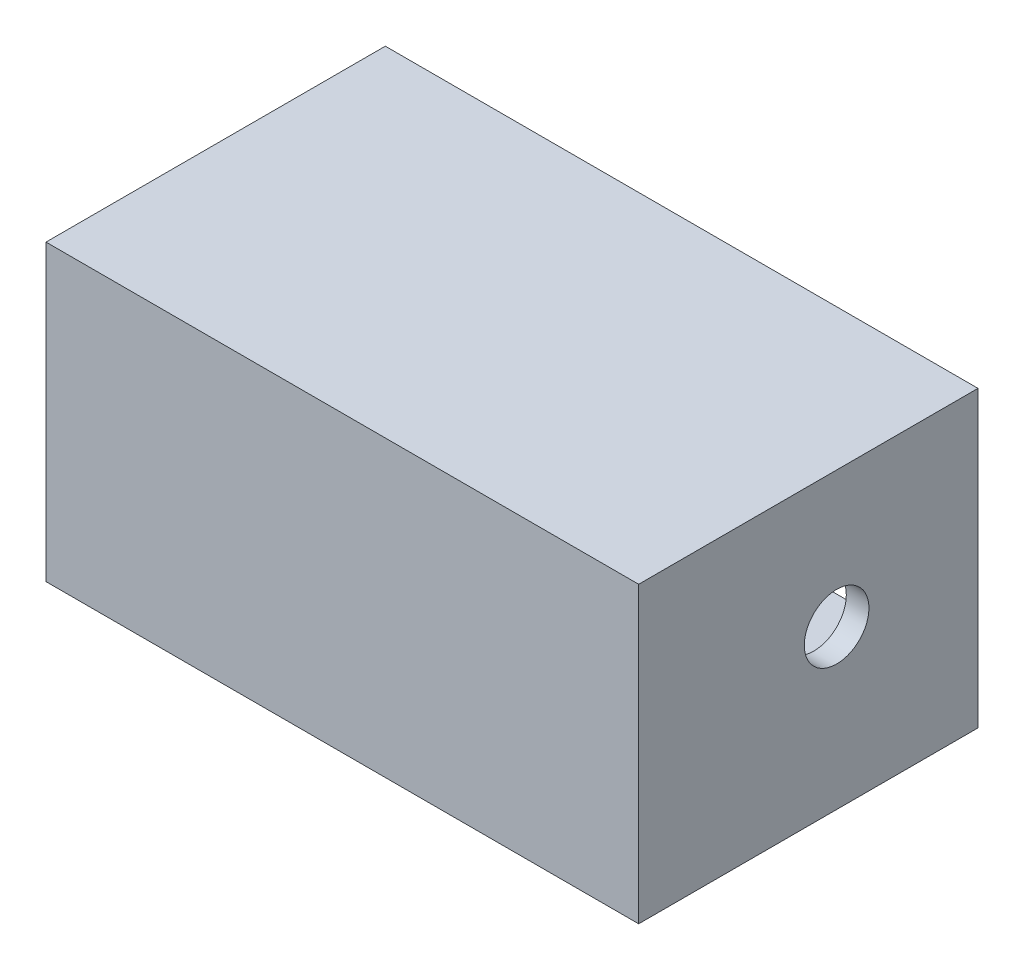
SolidWorks part; units mm, degrees
ref_plane "Front Plane" through (0, 0, 0) normal (0, 0, 1) x (1, 0, 0)
ref_plane "Top Plane" through (0, 0, 0) normal (0, 1, 0) x (1, 0, 0)
ref_plane "Right Plane" through (0, 0, 0) normal (1, 0, 0) x (0, 0, -1)
sketch "Sketch1" plane through (0, 0, 0) normal (0, 1, 0) x (1, 0, 0)
  line L1 (0, 0) -> (262, 0)
  line L2 (0, 0) -> (0, 150)
  line L3 (0, 150) -> (262, 150)
  line L4 (262, 0) -> (262, 150)
extrude "Boss-Extrude1" add sketch "Sketch1" along normal blind 20
sketch "Sketch2" plane through (0, 20, 0) normal (0, 1, 0) x (1, 0, 0)
  line L1 (0, 0) -> (262, 0)
  line L3 (10, 10) -> (252, 10)
  line L5 (262, 150) -> (0, 150) construction
  line L7 (0, 0) -> (0, 150)
  line L8 (0, 150) -> (10, 150)
  line L9 (10, 10) -> (10, 150)
  line L11 (262, 150) -> (252, 150)
  line L12 (262, 150) -> (262, 0)
  line L14 (252, 150) -> (252, 10)
extrude "Boss-Extrude2" add sketch "Sketch2" along normal blind 100
sketch "Sketch3" plane through (10, 0, 0) normal (1, 0, 0) x (0, 0, -1)
  circle A0 centre (87.5, 70) radius 14.2875
sketch "Sketch4" plane through (252, 0, 0) normal (1, 0, 0) x (0, 0, -1)
  circle A0 centre (87.5, 70) radius 14.2875
extrude "Cut-Extrude1" cut sketch "Sketch3" against normal through all
extrude "Cut-Extrude2" cut sketch "Sketch4" along normal through all
sketch "Sketch5" plane through (0, 120, 0) normal (0, 1, 0) x (1, 0, 0)
  line L1 (0, 0) -> (262, 0)
  line L2 (0, 0) -> (0, 150)
  line L3 (0, 150) -> (262, 150)
  line L4 (262, 0) -> (262, 150)
extrude "Boss-Extrude4" add sketch "Sketch5" along normal blind 10
